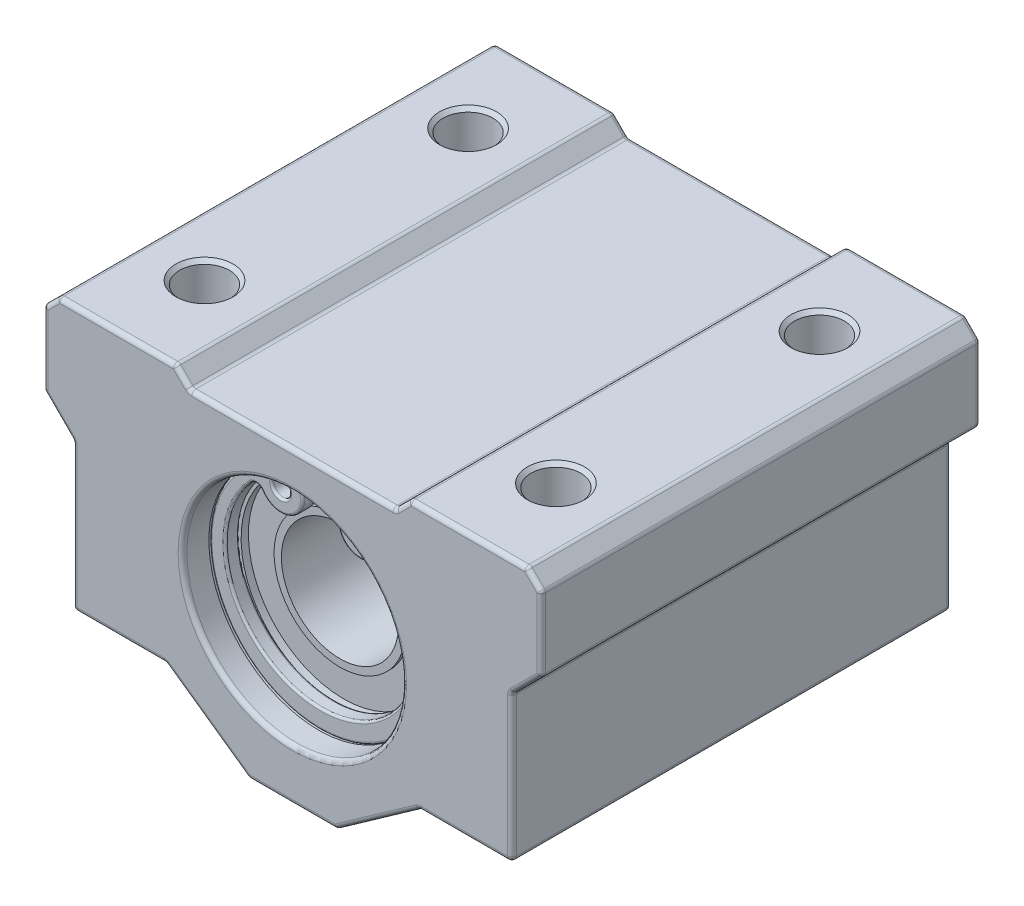
SolidWorks part; units mm, degrees
ref_plane "Piano frontale" through (0, 0, 0) normal (0, 0, 1) x (1, 0, 0)
ref_plane "Piano superiore" through (0, 0, 0) normal (0, 1, 0) x (1, 0, 0)
ref_plane "Piano destro" through (0, 0, 0) normal (1, 0, 0) x (0, 0, -1)
sketch "Schizzo1" plane through (0, 0, 0) normal (0, 0, 1) x (1, 0, 0)
  line L0 (0, 25) -> (0, -25) construction
  line L1 (-30, 0) -> (30, 0) construction
  line L2 (3, -11) -> (8.6667, -7)
  line L3 (8.6667, -7) -> (15, -7)
  line L4 (15, -7) -> (15, 3)
  line L5 (15, 3) -> (17, 5)
  line L6 (17, 5) -> (17, 10)
  line L8 (16, 11) -> (8, 11)
  line L9 (7, 10) -> (8, 11)
  line L10 (-17, 10) -> (17, 10) construction
  line L11 (-16, 11) -> (-17, 10)
  line L12 (16, 11) -> (17, 10)
  line L15 (-3, -11) -> (-8.6667, -7)
  line L16 (-8.6667, -7) -> (-15, -7)
  line L17 (-15, -7) -> (-15, 3)
  line L18 (-15, 3) -> (-17, 5)
  line L19 (-17, 5) -> (-17, 10)
  line L20 (-16, 11) -> (-8, 11)
  line L24 (-7, 10) -> (-8, 11)
  line L26 (-7, 10) -> (7, 10)
  line L27 (-3, -11) -> (3, -11)
  circle A0 centre (0, 0) radius 7.5
  point P3 (0, 0)
  point P6 (0, 0)
  point P8 (0, -11)
  point P17 (0, 10)
  point P55 (0, -7.6504)
  dimension "D4" = 15
  dimension "D5" = 6
  dimension "D2" = 7
  dimension "D1" = 45
  dimension "D3" = 35.218
  dimension "D6" = 1
  dimension "D8" = 30
  dimension "G" = 18
  dimension "T" = 6
  dimension "F" = 22
  dimension "W" = 34
  dimension "E" = 17
  dimension "h" = 11
  dimension "L1" = 8
extrude "Estrusione-Estrusione1" add sketch "Schizzo1" along normal mid plane 30
hole_wizard "Foro per Vite M4-1" positions "Schizzo3" profile "Schizzo4" hole size "M4" standard "ISO" end condition through all
sketch "Schizzo3" plane through (0, 11, 0) normal (0, 1, 0) x (1, 0, 0)
  line L3 (0, 0) -> (-18, 0) construction
  line L5 (0, 0) -> (0, 17) construction
  line L6 (-17, -15) -> (-17, 15) construction
  line L7 (-8, 15) -> (-16, 15) construction
  point P0 (-12, 9)
  dimension "D1" = 12
  dimension "D2" = 9
  dimension "D3" = 5
  dimension "D4" = 6
sketch "Schizzo4" plane through (-12, 11, -9) normal (1, 0, 0) x (0, 0, 1)
  line L0 (0, 0) -> (0, 22)
  line L1 (0, 22) -> (1.7, 22)
  line L2 (1.7, 22) -> (1.7, 0)
  line L5 (1.7, 0) -> (0, 0)
  line L11 (0, -6.35) -> (0, 107.95) construction
  dimension "Thru Hole Dia." = 3.4
  dimension "Thru Hole Depth" = 22
pattern_linear "Ripetizione a L1" count 2 spacing 24 along (1, 0, 0) count 2 spacing 18 along (0, 0, 1) of "Foro per Vite M4-1"
chamfer "Smusso1" distance 0.25 angle 45 4 edges at (-12, 11, 10.7) (12, 11, 10.7) (12, 11, -7.3) (-12, 11, -7.3)
chamfer "Smusso2" distance 0.5 angle 45 4 edges at (10.3, -7, -9) (10.3, -7, 9) (-13.7, -7, 9) (-13.7, -7, -9)
sketch "Schizzo6" plane through (0, 0, 0) normal (1, 0, 0) x (0, 0, -1)
  line L0 (-20, 0) -> (20, 0) construction
  line L3 (-12, 6.5) -> (-11.5, 6.5)
  line L4 (-11.5, 6.5) -> (-11.5, 4.5)
  line L9 (11.5, 6.5) -> (11.5, 4.5)
  line L13 (-12, 7.5) -> (-12, 6.5)
  line L14 (0, -1.396) -> (0, 15.3751) construction
  line L15 (-12, 7.5) -> (12, 7.5)
  line L18 (12, 7.5) -> (12, 6.5)
  line L19 (12, 6.5) -> (11.5, 6.5)
  line L20 (-11.5, 4.5) -> (-11.75, 4.5)
  line L21 (11.5, 4.5) -> (11.75, 4.5)
  line L22 (-11.75, 4.5) -> (-11.75, 0)
  line L23 (11.75, 4.5) -> (11.75, 0)
  line L24 (11.75, 0) -> (-11.75, 0)
  point P3 (0, 0)
  point P7 (0, 7.5)
  dimension "D1" = 24
  dimension "D2" = 1
  dimension "D3" = 0.5
  dimension "D4" = 0.25
  dimension "D5" = 4.5
  dimension "D6" = 7.5
revolve "Rivoluzione1" add sketch "Schizzo6" angle 360 about L0
fillet "Raccordo1" radius 0.3 56 edges at (-8, 11, 0) (16, 11, 0) (-7, 10, 0) (8, 11, 0) (7, 10, 0) (-16, 11, 0) (-17, 10, 0) (-17, 5, 0) (-15, 3, 0) (-15, -7, 0) (-8.6667, -7, 0) (17, 10, 0) (17, 5, 0) (15, -7, 0) (15, 3, 0) (8.6667, -7, 0) (-3, -11, 0) (3, -11, 0) (7.5, 0, 15) (-5.8333, -9, 15) (-11.8333, -7, 15) (-15, -2, 15) (-16, 4, 15) (-17, 7.5, 15) (-16.5, 10.5, 15) (-12, 11, 15) (-7.5, 10.5, 15) (0, 10, 15) (7.5, 10.5, 15) (12, 11, 15) (16.5, 10.5, 15) (17, 7.5, 15) (16, 4, 15) (15, -2, 15) (11.8333, -7, 15) (5.8333, -9, 15) (0, -11, 15) (7.5, 0, -15) (5.8333, -9, -15) (11.8333, -7, -15) (15, -2, -15) (16, 4, -15) (17, 7.5, -15) (16.5, 10.5, -15) (12, 11, -15) (7.5, 10.5, -15) (0, 10, -15) (-7.5, 10.5, -15) (-12, 11, -15) (-16.5, 10.5, -15) (-17, 7.5, -15) (-16, 4, -15) (-15, -2, -15) (-11.8333, -7, -15) (-5.8333, -9, -15) (0, -11, -15)
sketch "Schizzo8" plane through (0, 0, 0) normal (0, 0, 1) x (1, 0, 0)
  circle A0 centre (0, 0) radius 4
  dimension "D1" = 8
extrude "Taglio-Estrusione2" cut sketch "Schizzo8" against normal through all both and the other way through all
sketch "Schizzo7" plane through (0, 0, 0) normal (0, 0, 1) x (1, 0, 0)
  circle A0 centre (0, 0) radius 7.85
  dimension "D1" = 15.7
extrude "Taglio-Estrusione1" cut sketch "Schizzo7" along normal blind 1.1 from offset 12.1
mirror "Specchia1" about plane through (0, 0, 0) normal (0, 0, 1) of "Taglio-Estrusione1"
sketch "Schizzo9" plane through (0, 0, 0) normal (0, 0, 1) x (1, 0, 0)
  line L0 (-9.6311, 0) -> (8.8612, 0) construction
  line L1 (0, 22.577) -> (0, -2.423) construction
  line L2 (0, 0) -> (11.179, 22.4215) construction
  line L3 (0, 0) -> (-11.179, 22.4215) construction
  line L4 (-1.7195, 0.25) -> (1.6027, 0.25) construction
  arc A11 (-3.3688, 6.7568) -> (3.3688, 6.7568) centre (0, 0) ccw
  arc A12 (-4.7535, 4.6833) -> (4.7535, 4.6833) centre (0, 0.25) ccw
  arc A13 (-3.9658, 4.6103) -> (-3.3688, 6.7568) centre (-2.6995, 5.4144) ccw
  arc A14 (3.9658, 4.6103) -> (3.3688, 6.7568) centre (2.6995, 5.4144) cw
  circle A15 centre (-2.6995, 5.4144) radius 0.6
  circle A16 centre (2.6995, 5.4144) radius 0.6
  arc A17 (3.9658, 4.6103) -> (4.7535, 4.6833) centre (4.3879, 4.3423) cw
  arc A18 (-3.9658, 4.6103) -> (-4.7535, 4.6833) centre (-4.3879, 4.3423) ccw
  dimension "D1" = 0.25
  dimension "D2" = 53
  dimension "D3" = 15.1
  dimension "D6" = 3
  dimension "D5" = 13
  dimension "D7" = 1.2
  dimension "D8" = 0.5
  dimension "D4" = 26.5
extrude "Estrusione-Estrusione2" add sketch "Schizzo9" along normal blind 1 from offset 12.1 separate body
pattern_linear "Ripetizione a L2" count 2 spacing 25.2 along (0, 0, -1) of "Estrusione-Estrusione2"
fillet "Raccordo4" radius 0.15 16 edges at (3.2995, 5.4144, 13.1) (-2.0995, 5.4144, 13.1) (0, -7.55, 13.1) (-1.2543, 5.0124, 13.1) (0, -6.25, 13.1) (1.2543, 5.0124, 13.1) (3.2995, 5.4144, 12.1) (0, -6.25, 12.1) (-1.2543, 5.0124, 12.1) (0, -7.55, 12.1) (1.2543, 5.0124, 12.1) (-2.0995, 5.4144, 12.1) (-4.3417, 4.8401, 13.1) (4.3417, 4.8401, 13.1) (4.3417, 4.8401, 12.1) (-4.3417, 4.8401, 12.1)
fillet "Raccordo5" radius 0.15 16 edges at (3.2995, 5.4144, -12.1) (-2.0995, 5.4144, -12.1) (0, -7.55, -12.1) (-1.2543, 5.0124, -12.1) (0, -6.25, -12.1) (1.2543, 5.0124, -12.1) (3.2995, 5.4144, -13.1) (0, -6.25, -13.1) (-1.2543, 5.0124, -13.1) (0, -7.55, -13.1) (1.2543, 5.0124, -13.1) (-2.0995, 5.4144, -13.1) (-4.3417, 4.8401, -12.1) (4.3417, 4.8401, -12.1) (4.3417, 4.8401, -13.1) (-4.3417, 4.8401, -13.1)
